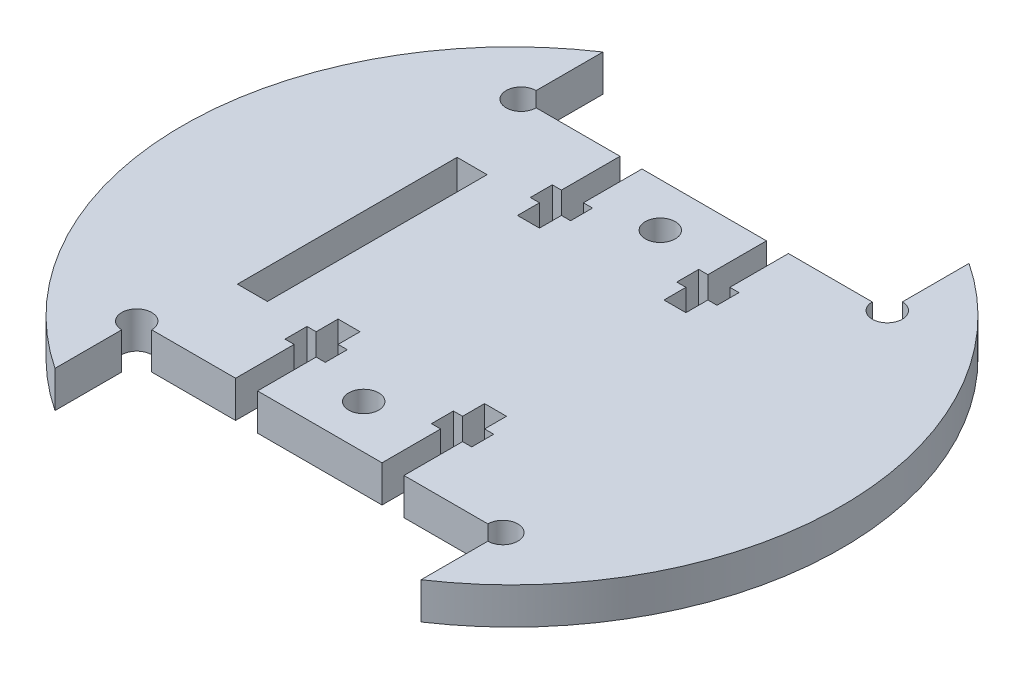
SolidWorks part; units mm, degrees
material "Acrílico (Impacto medio-alto)"
ref_plane "Piano frontale" through (0, 0, 0) normal (0, 0, 1) x (1, 0, 0)
ref_plane "Piano superiore" through (0, 0, 0) normal (0, 1, 0) x (1, 0, 0)
ref_plane "Piano destro" through (0, 0, 0) normal (1, 0, 0) x (0, 0, -1)
sketch "Schizzo1" plane through (0, 0, 0) normal (0, 1, 0) x (1, 0, 0)
  line L0 (-42.1632, 0) -> (43.9871, 0) construction
  line L1 (0, 26.25) -> (0, 0) construction
  line L2 (-25, 37.4166) -> (-25, 26.25)
  line L3 (-25, 26.25) -> (25, 26.25)
  line L4 (25, 37.4166) -> (25, 26.25)
  line L5 (0, 0) -> (0, -26.25) construction
  line L8 (-25, -37.4166) -> (-25, -26.25)
  line L9 (-25, -26.25) -> (25, -26.25)
  line L10 (25, -37.4166) -> (25, -26.25)
  arc A0 (-25, 37.4166) -> (-25, -37.4166) centre (0, 0) ccw
  arc A1 (25, -37.4166) -> (25, 37.4166) centre (0, 0) ccw
  point P3 (0, 45)
  point P8 (0, -45)
  dimension "D1" = 90
  dimension "D2" = 52.5
  dimension "D3" = 25
  dimension "D4" = 25
extrude "Estrusione-Estrusione1" add sketch "Schizzo1" along normal mid plane 5
sketch "Croquis1" plane through (0, -2.5, 0) normal (0, -1, 0) x (1, 0, 0)
  line L0 (-25, 26.25) -> (25, 26.25) construction
  line L1 (-11.5, 26.25) -> (-8.5, 26.25)
  line L2 (-11.5, 26.25) -> (-11.5, 18.25)
  line L3 (-11.5, 18.25) -> (-8.5, 18.25)
  line L4 (-8.5, 26.25) -> (-8.5, 18.25)
  line L5 (8.5, 26.25) -> (11.5, 26.25)
  line L6 (8.5, 26.25) -> (8.5, 18.25)
  line L7 (8.5, 18.25) -> (11.5, 18.25)
  line L8 (11.5, 26.25) -> (11.5, 18.25)
  line L9 (8.5, 31.25) -> (8.5, 27.25) construction
  line L10 (-11.5, 31.25) -> (-11.5, 27.25) construction
  line L11 (11.5, 27.25) -> (11.5, 31.25) construction
  line L12 (-12.75, 15.25) -> (-12.75, 18.25)
  line L13 (-12.75, 15.25) -> (-7.25, 15.25)
  line L14 (-12.75, 18.25) -> (-7.25, 18.25)
  line L15 (-7.25, 15.25) -> (-7.25, 18.25)
  line L16 (-12.75, 15.25) -> (-7.25, 18.25) construction
  line L17 (-12.75, 18.25) -> (-7.25, 15.25) construction
  line L18 (8.6009, 18.25) -> (11.3991, 18.25)
  line L19 (7.25, 15.25) -> (7.25, 18.25)
  line L20 (7.25, 15.25) -> (12.75, 15.25)
  line L21 (7.25, 18.25) -> (12.75, 18.25)
  line L22 (12.75, 15.25) -> (12.75, 18.25)
  line L23 (7.25, 15.25) -> (12.75, 18.25) construction
  line L24 (7.25, 18.25) -> (12.75, 15.25) construction
  line L25 (-45, 0) -> (45, 0) construction
  line L26 (-11.5, 15.25) -> (-8.5, 15.25)
  line L27 (-11.5, 15.25) -> (-11.5, 12.25)
  line L28 (-11.5, 12.25) -> (-8.5, 12.25)
  line L29 (-8.5, 15.25) -> (-8.5, 12.25)
  line L30 (8.5, 15.25) -> (11.5, 15.25)
  line L31 (8.5, 15.25) -> (8.5, 12.25)
  line L32 (8.5, 12.25) -> (11.5, 12.25)
  line L33 (11.5, 15.25) -> (11.5, 12.25)
  line L34 (7.25, -18.25) -> (12.75, -15.25) construction
  line L35 (7.25, -15.25) -> (12.75, -18.25) construction
  line L36 (-12.75, -18.25) -> (-7.25, -15.25) construction
  line L37 (-12.75, -15.25) -> (-7.25, -18.25) construction
  line L38 (11.5, -15.25) -> (11.5, -12.25)
  line L39 (8.5, -12.25) -> (11.5, -12.25)
  line L40 (8.5, -15.25) -> (8.5, -12.25)
  line L41 (8.5, -15.25) -> (11.5, -15.25)
  line L42 (-8.5, -15.25) -> (-8.5, -12.25)
  line L43 (-11.5, -12.25) -> (-8.5, -12.25)
  line L44 (-11.5, -15.25) -> (-11.5, -12.25)
  line L45 (-11.5, -15.25) -> (-8.5, -15.25)
  line L46 (12.75, -15.25) -> (12.75, -18.25)
  line L47 (7.25, -18.25) -> (12.75, -18.25)
  line L48 (7.25, -15.25) -> (12.75, -15.25)
  line L49 (7.25, -15.25) -> (7.25, -18.25)
  line L50 (8.6009, -18.25) -> (11.3991, -18.25)
  line L51 (-7.25, -15.25) -> (-7.25, -18.25)
  line L52 (-12.75, -18.25) -> (-7.25, -18.25)
  line L53 (-12.75, -15.25) -> (-7.25, -15.25)
  line L54 (-12.75, -15.25) -> (-12.75, -18.25)
  line L55 (11.5, -26.25) -> (11.5, -18.25)
  line L56 (8.5, -18.25) -> (11.5, -18.25)
  line L57 (8.5, -26.25) -> (8.5, -18.25)
  line L58 (8.5, -26.25) -> (11.5, -26.25)
  line L59 (-8.5, -26.25) -> (-8.5, -18.25)
  line L60 (-11.5, -18.25) -> (-8.5, -18.25)
  line L61 (-11.5, -26.25) -> (-11.5, -18.25)
  line L62 (-11.5, -26.25) -> (-8.5, -26.25)
  arc A0 (-25, 37.4166) -> (-25, -37.4166) centre (0, 0) ccw construction
  arc A1 (25, -37.4166) -> (25, 37.4166) centre (0, 0) ccw construction
  point P17 (-10, 16.75)
  point P18 (-10, 18.25)
  point P26 (10, 16.75)
  point P27 (10, 18.25)
  point P32 (10, 18.25)
  point P75 (10, -16.75)
  point P76 (-10, -16.75)
  line M3 (25, 26.25) -> (-25, 26.25)
  line M7 (-25, -26.25) -> (25, -26.25)
  dimension "D1" = 17
  dimension "D2" = 8
  dimension "D3" = 5.5
  dimension "D4" = 3
  dimension "D5" = 5.5
  dimension "D6" = 3
  dimension "D7" = 3
  dimension "D8" = 3
extrude "Cortar-Extruir4" cut sketch "Croquis1" against normal blind 10 contours L4 L2 L3 M3 | L13 L15 L14 L3 L12 | L33 L20 L31 L32 | L8 L6 L7 M3 | L44 L45 L42 L43 | L53 L54 L52 L51 L45 | L48 L49 L47 L46 L41 | L40 L41 L38 L39 | L57 L55 L47 M7 | L61 L59 L52 M7 | L27 L28 L29 L26
sketch "Croquis2" plane through (0, 2.5, 0) normal (0, 1, 0) x (1, 0, 0)
  line L1 (0, 20.25) -> (0, -20.25) construction
  line L2 (-25, 26.25) -> (-25, -26.25) construction
  circle A7 centre (0, 20.25) radius 2.05
  circle A8 centre (0, -20.25) radius 2.05
  point P2 (-25, 0)
  point P3 (0, 0)
  dimension "D1" = 4.1
  dimension "D2" = 40.5
extrude "Cortar-Extruir5" cut sketch "Croquis2" against normal through all
sketch "Sketch3" plane through (0, 2.5, 0) normal (0, 1, 0) x (1, 0, 0)
  line L0 (0, 26.25) -> (0, -26.25) construction
  line L1 (-22.5, -15) -> (-18.4, -15)
  line L2 (-22.5, -15) -> (-22.5, 15)
  line L3 (-22.5, 15) -> (-18.4, 15)
  line L4 (-18.4, -15) -> (-18.4, 15)
  line L5 (-22.5, -15) -> (-18.4, 15) construction
  line L6 (-22.5, 15) -> (-18.4, -15) construction
  line L7 (8.5, 26.25) -> (-8.5, 26.25) construction
  line L8 (-8.5, -26.25) -> (8.5, -26.25) construction
  point P4 (-20.45, 0)
  point P11 (0, 0)
  dimension "D1" = 30
  dimension "D2" = 4.1
  dimension "D3" = 18.4
extrude "Cut-Extrude1" cut sketch "Sketch3" against normal up to next
sketch "Sketch4" plane through (0, 2.5, 0) normal (0, 1, 0) x (1, 0, 0)
  circle A0 centre (-25, 26.25) radius 2.05
  circle A1 centre (-25, -26.25) radius 2.05
  circle A2 centre (25, -26.25) radius 2.05
  circle A3 centre (25, 26.25) radius 2.05
  dimension "D1" = 4.1
extrude "Cut-Extrude2" cut sketch "Sketch4" against normal up to next
